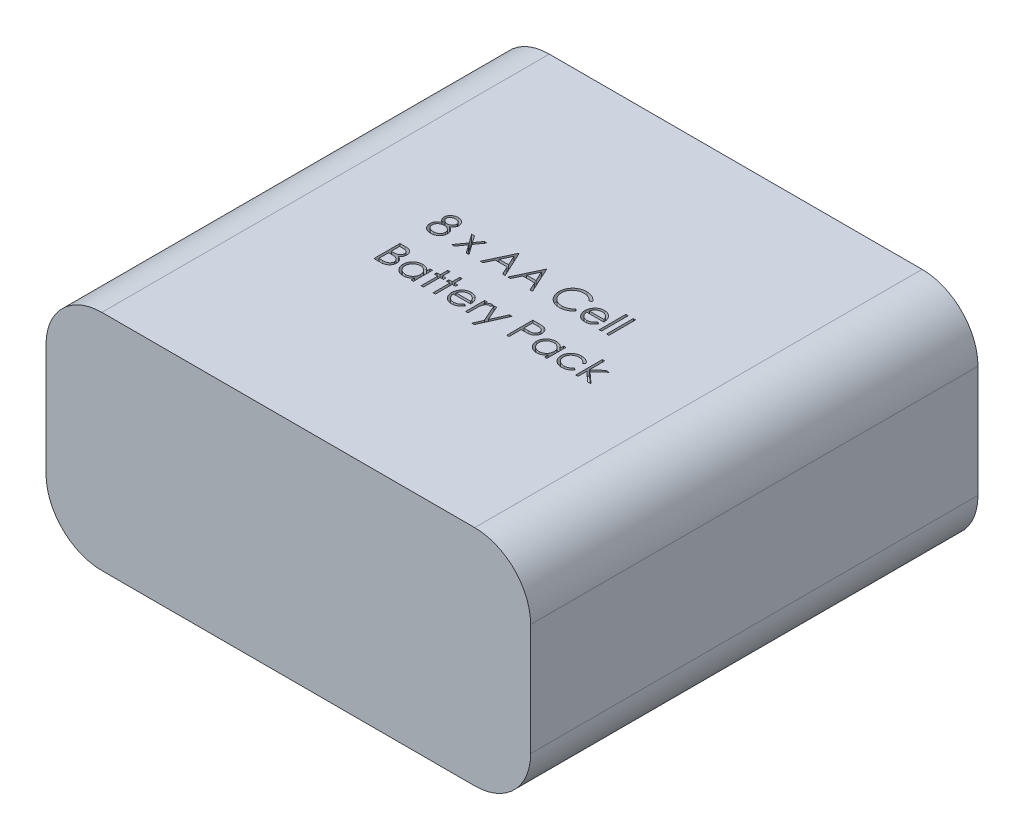
SolidWorks part; units mm, degrees
ref_plane "Front Plane" through (0, 0, 0) normal (0, 0, 1) x (1, 0, 0)
ref_plane "Top Plane" through (0, 0, 0) normal (0, 1, 0) x (1, 0, 0)
ref_plane "Right Plane" through (0, 0, 0) normal (1, 0, 0) x (0, 0, -1)
sketch "Sketch1" plane through (0, 0, 0) normal (0, 0, 1) x (1, 0, 0)
  line L1 (0, 0) -> (65, 0)
  line L2 (0, 0) -> (0, 30)
  line L3 (0, 30) -> (65, 30)
  line L4 (65, 0) -> (65, 30)
  dimension "D1" = 65
  dimension "D2" = 30
extrude "Boss-Extrude1" add sketch "Sketch1" against normal blind 60
fillet "Fillet1" radius 7.5 4 edges at (0, 0, -30) (0, 30, -30) (65, 0, -30) (65, 30, -30)
sketch "Sketch2" plane through (0, 30, 0) normal (0, 1, 0) x (1, 0, 0)
  text T0 "8 x AA Cell \r\nBattery Pack"
extrude "Cut-Extrude1" cut sketch "Sketch2" against normal blind 1
